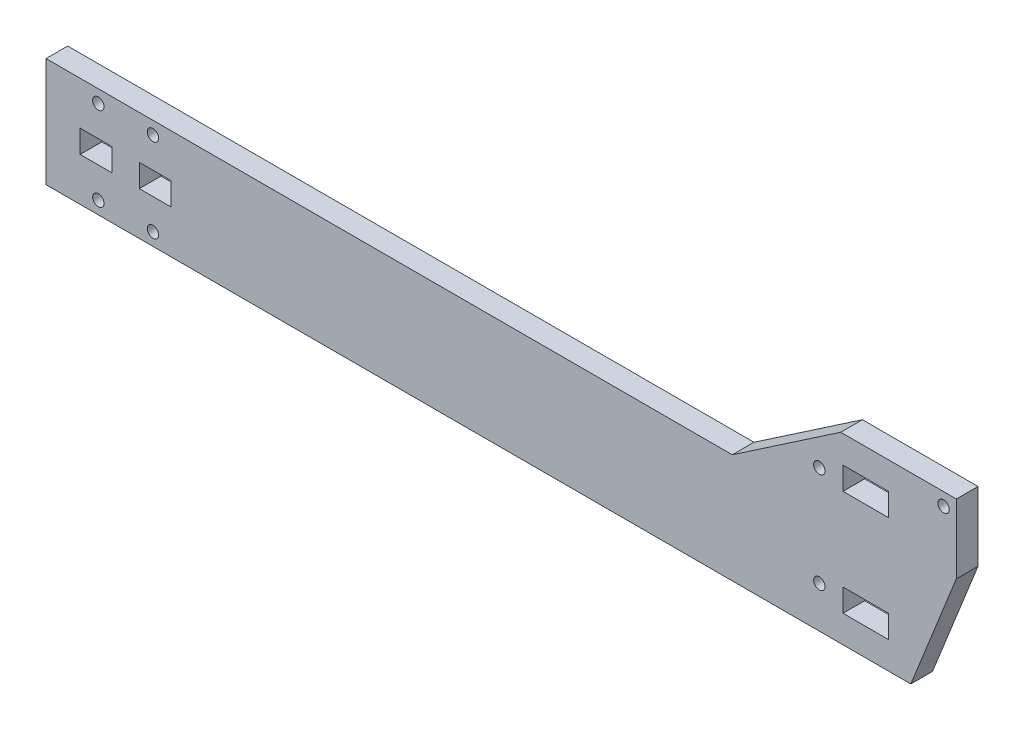
SolidWorks part; units mm, degrees
ref_plane "Front Plane" through (0, 0, 0) normal (0, 0, 1) x (1, 0, 0)
ref_plane "Top Plane" through (0, 0, 0) normal (0, 1, 0) x (1, 0, 0)
ref_plane "Right Plane" through (0, 0, 0) normal (1, 0, 0) x (0, 0, -1)
sketch "Sketch1" plane through (0, 0, 0) normal (0, 0, 1) x (1, 0, 0)
  line L0 (174.6, 40.2) -> (150.7765, 24)
  line L1 (174.6, 40.2) -> (200, 40.2)
  line L2 (200, 40.2) -> (200, 25)
  line L3 (200, 25) -> (190, 0)
  line L4 (190, 0) -> (0, 0)
  line L5 (150.7765, 24) -> (0, 24)
  line L6 (0, 24) -> (0, 0)
  line L7 (174.6, 40.2) -> (174.6, 35.1) construction
  line L8 (174.6, 35.1) -> (167.1, 35.1) construction
  dimension "D1" = 25.4
  dimension "D2" = 200
  dimension "D3" = 24
  dimension "D4" = 40.2
  dimension "D5" = 10
  dimension "D6" = 5.1
  dimension "D7" = 7.5
  dimension "D8" = 25
extrude "Boss-Extrude1" add sketch "Sketch1" along normal blind 4.7625
sketch "Sketch2" plane through (0, 0, 4.7625) normal (0, 0, 1) x (1, 0, 0)
  line L0 (200, 25) -> (200, 40.2) construction
  line L1 (175.1, 29.2) -> (185.1, 29.2)
  line L2 (175.1, 29.2) -> (175.1, 34.2)
  line L3 (175.1, 34.2) -> (185.1, 34.2)
  line L4 (185.1, 29.2) -> (185.1, 34.2)
  line L5 (175.1, 29.2) -> (185.1, 34.2) construction
  line L6 (175.1, 34.2) -> (185.1, 29.2) construction
  line L7 (200, 40.2) -> (174.6, 40.2) construction
  line L8 (11, 12) -> (24, 12) construction
  line L9 (175.1, 11) -> (185.1, 11)
  line L10 (175.1, 11) -> (175.1, 6)
  line L11 (175.1, 6) -> (185.1, 6)
  line L12 (185.1, 11) -> (185.1, 6)
  line L13 (175.1, 11) -> (185.1, 6) construction
  line L14 (175.1, 6) -> (185.1, 11) construction
  line L15 (7.5, 14.5) -> (14.5, 14.5)
  line L16 (7.5, 14.5) -> (7.5, 9.5)
  line L17 (7.5, 9.5) -> (14.5, 9.5)
  line L18 (14.5, 14.5) -> (14.5, 9.5)
  line L19 (7.5, 14.5) -> (14.5, 9.5) construction
  line L20 (7.5, 9.5) -> (14.5, 14.5) construction
  line L21 (20.5, 14.5) -> (27.5, 14.5)
  line L22 (20.5, 14.5) -> (20.5, 9.5)
  line L23 (20.5, 9.5) -> (27.5, 9.5)
  line L24 (27.5, 14.5) -> (27.5, 9.5)
  line L25 (20.5, 14.5) -> (27.5, 9.5) construction
  line L26 (20.5, 9.5) -> (27.5, 14.5) construction
  line L27 (17.5, 12) -> (0, 12) construction
  line L28 (0, 24) -> (0, 0) construction
  line L29 (200, 25) -> (200, 40.2) construction
  line L30 (0, 0) -> (190, 0) construction
  line L31 (150.7765, 24) -> (0, 24) construction
  line L32 (11.5, 2.8) -> (23.5, 2.8) construction
  line L33 (11.5, 2.8) -> (11.5, 21.2) construction
  line L34 (11.5, 21.2) -> (23.5, 21.2) construction
  line L35 (23.5, 2.8) -> (23.5, 21.2) construction
  line L36 (11.5, 2.8) -> (23.5, 21.2) construction
  line L37 (11.5, 21.2) -> (23.5, 2.8) construction
  circle A0 centre (169.9, 31.1) radius 1.25
  circle A1 centre (197.2, 37.4) radius 1.25
  circle A3 centre (169.9, 9.1) radius 1.25
  circle A4 centre (23.5, 21.2) radius 1.25
  circle A5 centre (11.5, 21.2) radius 1.25
  circle A6 centre (11.5, 2.8) radius 1.25
  circle A7 centre (23.5, 2.8) radius 1.25
  point P0 (180.1, 31.7)
  point P9 (180.1, 8.5)
  point P14 (11, 12)
  point P19 (24, 12)
  dimension "D12" = 2.5
  dimension "D19" = 2.5
  dimension "D1" = 5
  dimension "D2" = 10
  dimension "D3" = 14.9
  dimension "D4" = 6
  dimension "D5" = 18.2
  dimension "D6" = 6
  dimension "D7" = 5
  dimension "D8" = 7
  dimension "D9" = 17.5
  dimension "D10" = 2.8
  dimension "D11" = 2.8
  dimension "D13" = 30.1
  dimension "D14" = 9.1
  dimension "D15" = 9.1
  dimension "D17" = 12
  dimension "D18" = 2.8
extrude "Cut-Extrude1" cut sketch "Sketch2" against normal through all
sketch "Sketch3" plane through (0, 0, 4.7625) normal (0, 0, 1) x (1, 0, 0)
  line L0 (14.5, 14.5) -> (7.5, 14.5) construction
  line L1 (14.5, 9.5) -> (14.5, 14.5) construction
  line L2 (7.5, 9.5) -> (14.5, 9.5) construction
  line L3 (7.5, 14.5) -> (7.5, 9.5) construction
  line L4 (20.5, 14.5) -> (20.5, 9.5) construction
  line L5 (27.5, 14.5) -> (20.5, 14.5) construction
  line L6 (27.5, 9.5) -> (27.5, 14.5) construction
  line L7 (0, 24) -> (0, 0)
  line L8 (0, 0) -> (190, 0)
  line L9 (190, 0) -> (200, 25)
  line L10 (200, 25) -> (200, 40.2)
  line L11 (200, 40.2) -> (174.6, 40.2)
  line L12 (174.6, 40.2) -> (150.7765, 24)
  line L13 (150.7765, 24) -> (0, 24)
  line L14 (0, 24) -> (0, 0)
  line L15 (0, 0) -> (190, 0)
  line L16 (190, 0) -> (200, 25)
  line L17 (200, 25) -> (200, 40.2)
  line L18 (200, 40.2) -> (174.6, 40.2)
  line L19 (174.6, 40.2) -> (150.7765, 24)
  line L20 (150.7765, 24) -> (0, 24)
  line L21 (20.5, 9.5) -> (27.5, 9.5) construction
  line L22 (185.1, 29.2) -> (185.1, 34.2) construction
  line L23 (185.1, 34.2) -> (175.1, 34.2) construction
  line L24 (175.1, 34.2) -> (175.1, 29.2) construction
  line L25 (175.1, 29.2) -> (185.1, 29.2) construction
  line L26 (175.1, 11) -> (175.1, 6) construction
  line L27 (185.1, 11) -> (175.1, 11) construction
  line L28 (185.1, 6) -> (185.1, 11) construction
  line L29 (175.1, 6) -> (185.1, 6) construction
  line L30 (14.5, 14.5) -> (7.5, 14.5)
  line L31 (14.5, 9.5) -> (14.5, 14.5)
  line L32 (7.5, 9.5) -> (14.5, 9.5)
  line L33 (7.5, 14.5) -> (7.5, 9.5)
  line L34 (20.5, 14.5) -> (20.5, 9.5)
  line L35 (27.5, 14.5) -> (20.5, 14.5)
  line L36 (27.5, 9.5) -> (27.5, 14.5)
  line L37 (20.5, 9.5) -> (27.5, 9.5)
  line L38 (185.1, 29.2) -> (185.1, 34.2)
  line L39 (185.1, 34.2) -> (175.1, 34.2)
  line L40 (175.1, 34.2) -> (175.1, 29.2)
  line L41 (175.1, 29.2) -> (185.1, 29.2)
  line L42 (175.1, 11) -> (175.1, 6)
  line L43 (185.1, 11) -> (175.1, 11)
  line L44 (185.1, 6) -> (185.1, 11)
  line L45 (175.1, 6) -> (185.1, 6)
  circle A0 centre (23.5, 21.2) radius 1.25 construction
  circle A1 centre (11.5, 21.2) radius 1.25 construction
  circle A2 centre (11.5, 2.8) radius 1.25 construction
  circle A3 centre (23.5, 2.8) radius 1.25 construction
  circle A4 centre (169.9, 31.1) radius 1.25 construction
  circle A5 centre (197.2, 37.4) radius 1.25 construction
  circle A6 centre (169.9, 9.1) radius 1.25 construction
  circle A7 centre (23.5, 21.2) radius 1.25
  circle A8 centre (11.5, 21.2) radius 1.25
  circle A9 centre (11.5, 2.8) radius 1.25
  circle A10 centre (23.5, 2.8) radius 1.25
  circle A11 centre (169.9, 31.1) radius 1.25
  circle A12 centre (197.2, 37.4) radius 1.25
  circle A13 centre (169.9, 9.1) radius 1.25
  dimension "D1" = 0
